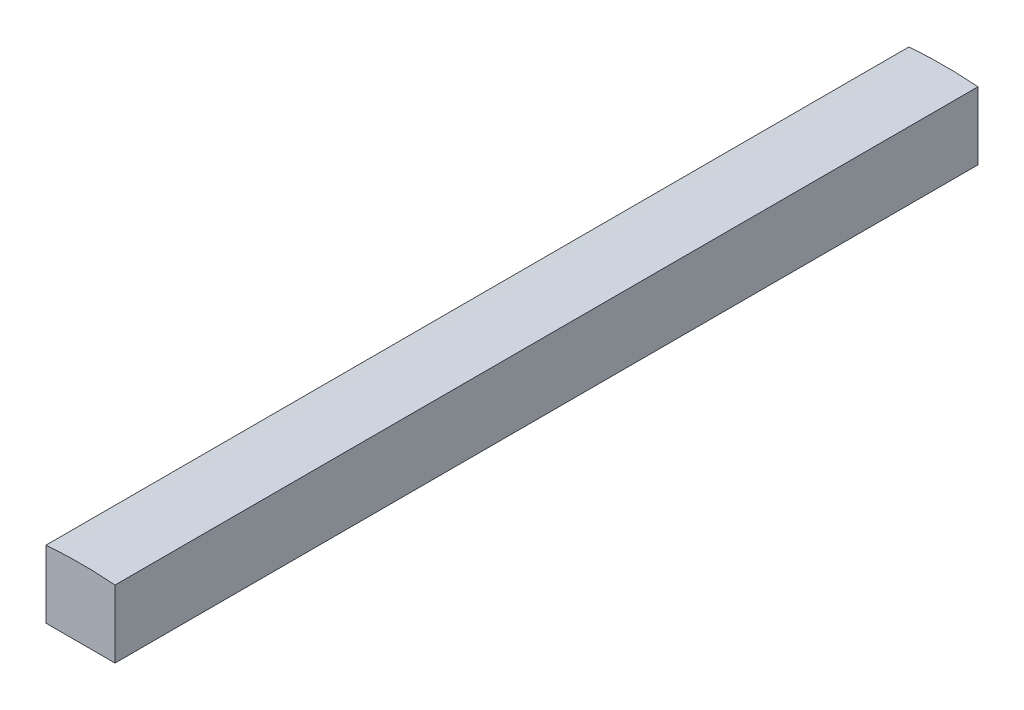
SolidWorks part; units mm, degrees
ref_plane "Ebene vorne" through (0, 0, 0) normal (0, 0, 1) x (1, 0, 0)
ref_plane "Ebene oben" through (0, 0, 0) normal (0, 1, 0) x (1, 0, 0)
ref_plane "Ebene rechts" through (0, 0, 0) normal (1, 0, 0) x (0, 0, -1)
sketch "Skizze1" plane through (0, 0, 0) normal (0, 0, 1) x (1, 0, 0)
  line L1 (-20, 206) -> (-20, 245.1856)
  line L2 (20, 206) -> (20, 245.1856)
  line L7 (-20, 206) -> (20, 206)
  arc A0 (20, 245.1856) -> (-20, 245.1856) centre (0, 0) ccw
  point P3 (-20, 0)
  point P4 (0, 246)
  point P5 (-20, 246)
  point P6 (20, 0)
  point P7 (0, 0)
  point P8 (20, 246)
  point P12 (0, 246)
  point P13 (0, 0)
  point P14 (0, 0)
  point P15 (0, 206)
  point P16 (20, 206)
  point P17 (20, 206)
  dimension "D1" = 492
  dimension "D3" = 246
  dimension "D2" = 40
  dimension "D4" = 40
extrude "Aufsatz-Linear austragen1" add sketch "Skizze1" along normal blind 500 contours A0 L1 L7 L2
